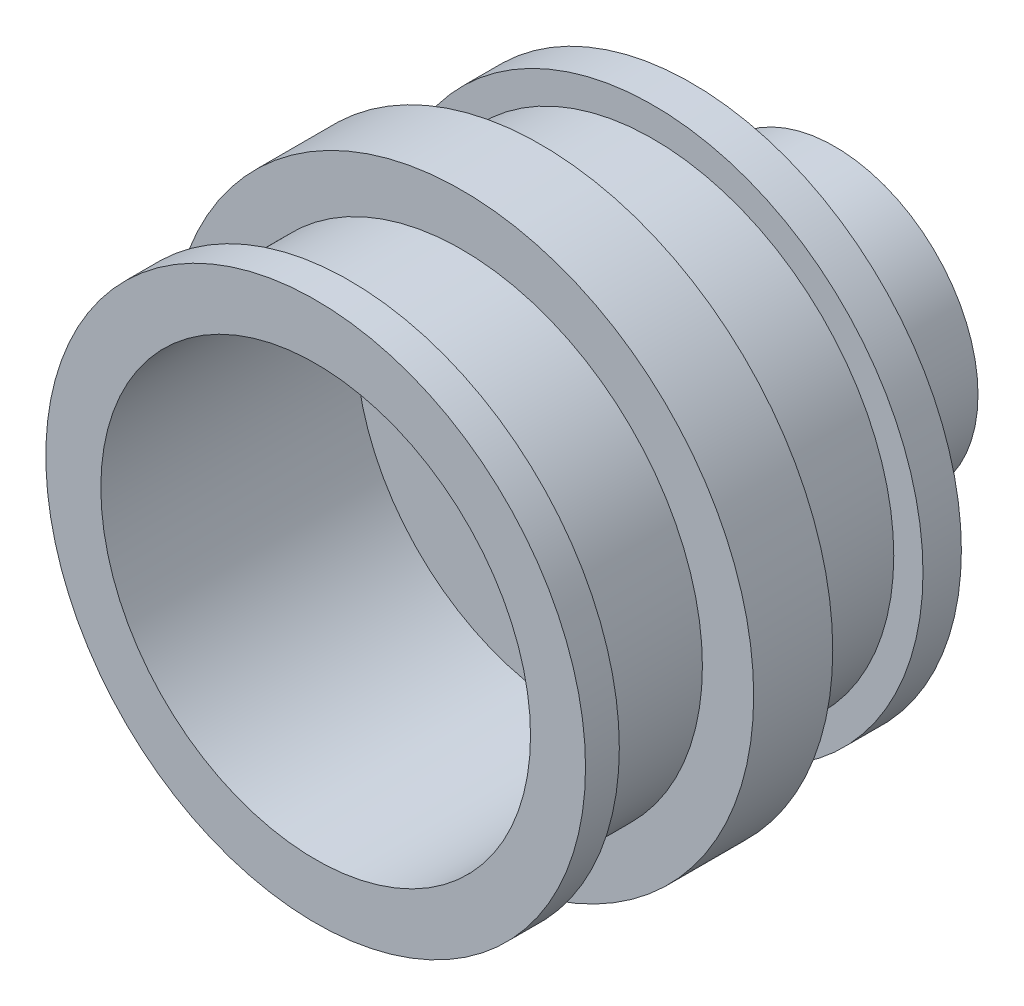
SolidWorks part; units mm, degrees
ref_plane "Płaszczyzna przednia" through (0, 0, 0) normal (0, 0, 1) x (1, 0, 0)
ref_plane "Płaszczyzna górna" through (0, 0, 0) normal (0, 1, 0) x (1, 0, 0)
ref_plane "Płaszczyzna prawa" through (0, 0, 0) normal (1, 0, 0) x (0, 0, -1)
sketch "Szkic1" plane through (0, 0, 0) normal (0, 0, 1) x (1, 0, 0)
  circle A0 centre (0, 0) radius 9.42
  dimension "D1" = 18.84
extrude "Dodanie-wyciągnięcie1" add sketch "Szkic1" along normal blind 1.34
sketch "Szkic2" plane through (0, 0, 1.34) normal (0, 0, 1) x (1, 0, 0)
  circle A0 centre (0, 0) radius 8.4
extrude "Dodanie-wyciągnięcie2" add sketch "Szkic2" along normal blind 3.92
sketch "Szkic3" plane through (0, 0, 5.26) normal (0, 0, 1) x (1, 0, 0)
  circle A0 centre (0, 0) radius 10.19
extrude "Dodanie-wyciągnięcie3" add sketch "Szkic3" along normal blind 2.76
sketch "Szkic4" plane through (0, 0, 8.02) normal (0, 0, 1) x (1, 0, 0)
  circle A0 centre (0, 0) radius 8.4
extrude "Dodanie-wyciągnięcie4" add sketch "Szkic4" along normal blind 3.92
sketch "Szkic5" plane through (0, 0, 11.94) normal (0, 0, 1) x (1, 0, 0)
  circle A0 centre (0, 0) radius 9.42
extrude "Dodanie-wyciągnięcie5" add sketch "Szkic5" along normal blind 1.18
sketch "Szkic6" plane through (0, 0, 13.12) normal (0, 0, 1) x (1, 0, 0)
  circle A0 centre (0, 0) radius 7.5
extrude "Wytnij-wyciągnięcie1" cut sketch "Szkic6" against normal blind 8.9
sketch "Szkic7" plane through (0, 0, 0) normal (0, 0, -1) x (-1, 0, 0)
  circle A0 centre (0, 0) radius 1.5
extrude "Wytnij-wyciągnięcie2" cut sketch "Szkic7" against normal up to next
sketch "Croquis1" plane through (0, 0, 0) normal (0, 0, -1) x (-1, 0, 0)
  circle A0 centre (0, 0) radius 5
  circle A1 centre (0, 0) radius 1.5 construction
  circle A2 centre (0, 0) radius 1.5
  dimension "D1" = 10
extrude "Saliente-Extruir1" add sketch "Croquis1" along normal blind 5
ref_plane "Plano1" through (0, 0, 0) normal (0, 1, 0) x (1, 0, 0)
sketch "Croquis2" plane through (0, 0, 0) normal (0, 1, 0) x (1, 0, 0)
  circle A0 centre (0, 2.3672) radius 0.635
  dimension "D1" = 1.27
extrude "Cortar-Extruir1" cut sketch "Croquis2" against normal through all both and the other way through all
